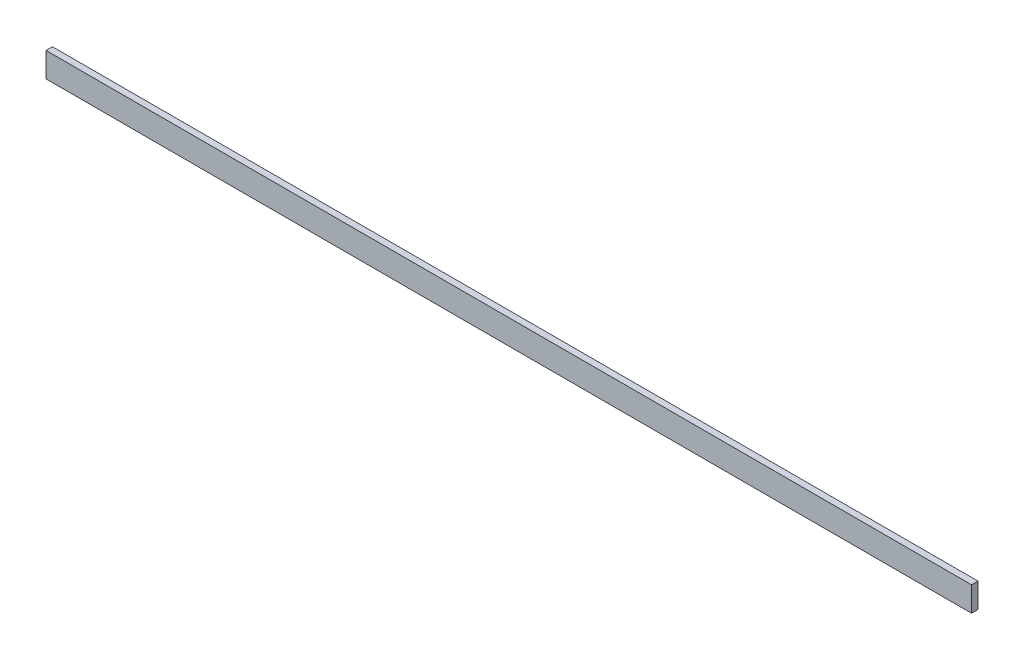
SolidWorks part; units mm, degrees
ref_plane "Front Plane" through (0, 0, 0) normal (0, 0, 1) x (1, 0, 0)
ref_plane "Top Plane" through (0, 0, 0) normal (0, 1, 0) x (1, 0, 0)
ref_plane "Right Plane" through (0, 0, 0) normal (1, 0, 0) x (0, 0, -1)
sketch "Sketch1" plane through (0, 0, 0) normal (0, 0, 1) x (1, 0, 0)
  line L0 (0, 0) -> (1437.2498, 0)
  line L1 (1437.2498, 0) -> (1437.2498, 38.2926)
  line L2 (1437.2498, 38.2926) -> (0, 38.2926)
  line L3 (0, 38.2926) -> (0, 0)
extrude "Boss-Extrude1" add sketch "Sketch1" along normal blind 10
